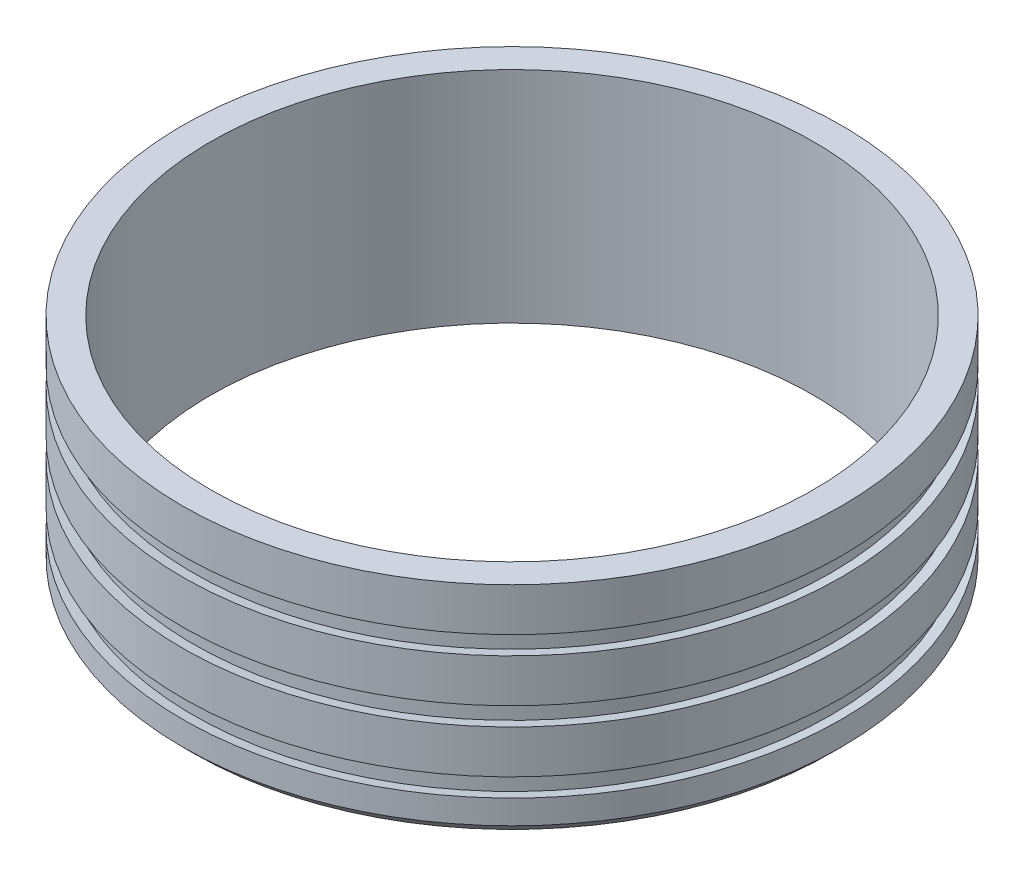
SolidWorks part; units mm, degrees
material "ABS"
ref_plane "Front Plane" through (0, 0, 0) normal (0, 0, 1) x (1, 0, 0)
ref_plane "Top Plane" through (0, 0, 0) normal (0, 1, 0) x (1, 0, 0)
ref_plane "Right Plane" through (0, 0, 0) normal (1, 0, 0) x (0, 0, -1)
sketch "Sketch1" plane through (0, 0, 0) normal (0, 1, 0) x (1, 0, 0)
  circle A0 centre (0, 0) radius 76.25
  circle A1 centre (0, 0) radius 69.75
  dimension "D2" = 152.5
  dimension "D1" = 6.5
extrude "Boss-Extrude1" add sketch "Sketch1" along normal blind 50.8
sketch "Sketch2" plane through (0, 0, 0) normal (0, 0, 1) x (1, 0, 0)
  line L0 (-76.25, 40.8) -> (-76.25, 36.55) construction
  line L1 (-76.25, 40.8) -> (-76.25, 36.55)
  line L2 (-76.25, 50.8) -> (-76.25, 0) construction
  line L19 (0, 0) -> (0, 50.8) construction
  line L20 (-76.25, 0) -> (76.25, 0) construction
  line L21 (69.75, 50.8) -> (-69.75, 50.8) construction
  line L22 (-76.25, 40.8) -> (-73.75, 41.2408)
  line L23 (-73.75, 41.2408) -> (-73.75, 36.1092)
  line L24 (-73.75, 38.675) -> (-76.25, 38.675) construction
  line L25 (-76.25, 36.55) -> (-73.75, 36.1092)
  line L26 (-73.75, 26.9908) -> (-73.75, 21.8592)
  line L27 (-76.25, 22.3) -> (-73.75, 21.8592)
  line L28 (-76.25, 26.55) -> (-76.25, 22.3)
  line L29 (-76.25, 26.55) -> (-73.75, 26.9908)
  line L30 (-73.75, 12.7408) -> (-73.75, 7.6092)
  line L31 (-76.25, 8.05) -> (-73.75, 7.6092)
  line L32 (-76.25, 12.3) -> (-76.25, 8.05)
  line L33 (-76.25, 12.3) -> (-73.75, 12.7408)
  dimension "D2" = 2.5
  dimension "D3" = 100
  dimension "D1" = 4.25
  dimension "D5" = 10
  dimension "D6" = 10
  dimension "D4" = 3
revolve "Cut-Revolve1" cut sketch "Sketch2" angle 360 about L19
chamfer "Chamfer1" distance 2.5 angle 45 1 edges at (0, 0, 76.25)
